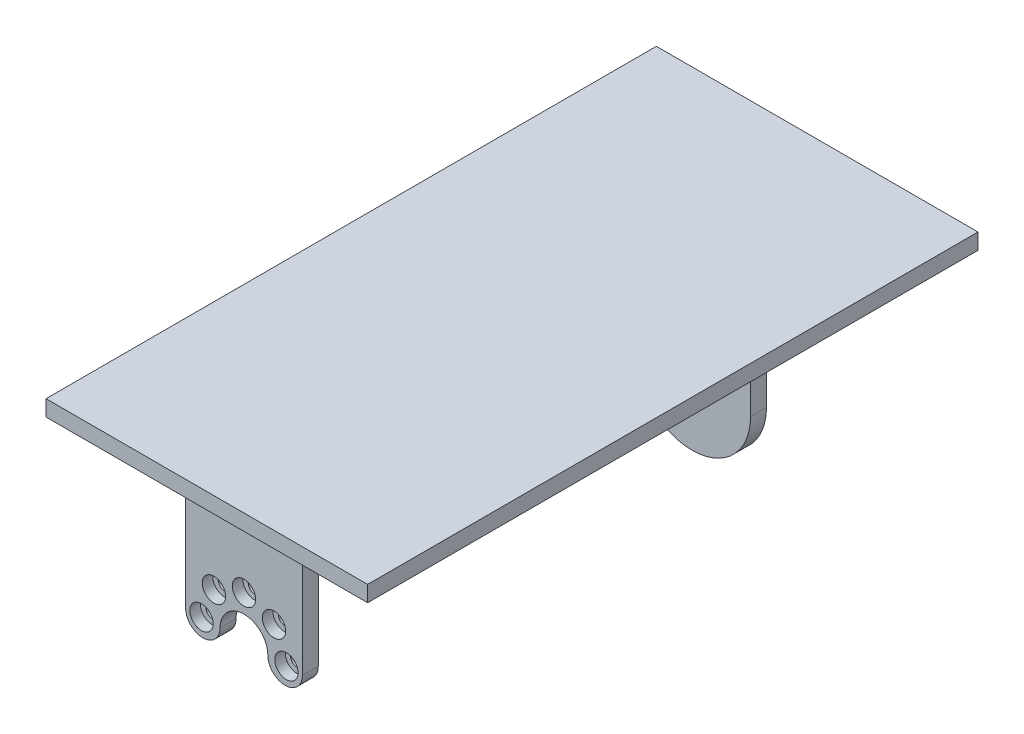
SolidWorks part; units mm, degrees
ref_plane "Plano frontal" through (0, 0, 0) normal (0, 0, 1) x (1, 0, 0)
ref_plane "Plano superior" through (0, 0, 0) normal (0, 1, 0) x (1, 0, 0)
ref_plane "Plano direito" through (0, 0, 0) normal (1, 0, 0) x (0, 0, -1)
sketch "Esboço1" plane through (0, 0, 0) normal (0, 0, 1) x (1, 0, 0)
  line L0 (11, 0) -> (11, 25)
  line L1 (11, 25) -> (-11, 25)
  line L2 (-11, 25) -> (-11, 0)
  arc A3 (11, 0) -> (4.5, 0) centre (7.75, 0) cw
  arc A8 (4.5, 0) -> (-4.5, 0) centre (0, 0) ccw
  arc A10 (-4.5, 0) -> (-11, 0) centre (-7.75, 0) cw
  dimension "D1" = 25
extrude "Ressalto-extrusão1" add sketch "Esboço1" along normal blind 3
sketch "Esboço2" plane through (0, 25, 0) normal (0, 1, 0) x (1, 0, 0)
  line L1 (-30.3, -10) -> (30.3, -10)
  line L2 (-30.3, -10) -> (-30.3, 105)
  line L3 (-30.3, 105) -> (30.3, 105)
  line L4 (30.3, -10) -> (30.3, 105)
  line L5 (11, -3) -> (-11, -3) construction
  point P7 (0, -3)
  point P8 (0, -10)
  dimension "D1" = 115
  dimension "D2" = 60.6
  dimension "D3" = 7
extrude "Ressalto-extrusão2" add sketch "Esboço2" along normal blind 3
ref_plane "Plano1" through (0, 0, -81.45) normal (0, 0, -1) x (-1, 0, 0)
sketch "Esboço3" plane through (0, 0, -81.45) normal (0, 0, -1) x (-1, 0, 0)
  line L1 (-11, 0) -> (-11, 25)
  line L2 (-11, 25) -> (11, 25)
  line L3 (11, 25) -> (11, 0)
  arc A0 (-11, 0) -> (11, 0) centre (0, 0) ccw
  dimension "D1" = 22
extrude "Ressalto-extrusão3" add sketch "Esboço3" along normal blind 3
hole_wizard "Rebaixo para SHCS M21" positions "Esboço4" profile "Esboço5" counterbore size "M2" standard "Ansi Metric"
sketch "Esboço4" plane through (0, 0, 3) normal (0, 0, 1) x (1, 0, 0)
  arc A0 (8.8, 0) -> (7.2, 0) centre (8, 0) ccw construction
  point P0 (8, 0)
sketch "Esboço5" plane through (8, 0, 3) normal (1, 0, 0) x (0, -1, 0)
  line L0 (0, 0) -> (0, 3)
  line L1 (0, 3) -> (1.2, 3)
  line L3 (1.2, 3) -> (1.2, 2)
  line L4 (1.2, 2) -> (2.2, 2)
  line L5 (2.2, 2) -> (2.2, 0)
  line L7 (2.2, 0) -> (0, 0)
  line L11 (0, -6.35) -> (0, 107.95) construction
  dimension "Thru Hole Dia." = 2.4
  dimension "Thru Hole Depth" = 3
  dimension "C'Bore Dia." = 4.4
  dimension "C'Bore Depth" = 2
pattern_circular "PadrãoCircular1" count 5 over 180 about axis through (0, 0, 0) along (0, 0, 1) of "Rebaixo para SHCS M21"
sketch "Esboço6" plane through (0, 0, 0) normal (1, 0, 0) x (0, 0, -1)
  line L0 (-10, 25) -> (-3, 25) construction
  line L3 (-3, 25) -> (-3, 18) construction
  line L4 (-3, 0) -> (-3, 25) construction
  line L5 (-3, 18) -> (-10, 25)
rib "Nervura1" sketch "Esboço6" sketch "Esboço6" thickness 15 extrusion direction parallel to sketch draft on no parameters "D1"=15
sketch "Esboço7" plane through (0, 0, 3) normal (0, 0, 1) x (1, 0, 0)
  line L0 (-7.5, 25) -> (7.5, 25) construction
  line L1 (-5, 25) -> (5, 25)
  line L2 (-5, 25) -> (-5, 18)
  line L3 (-5, 18) -> (5, 18)
  line L4 (5, 25) -> (5, 18)
  line L5 (7.5, 18) -> (-7.5, 18) construction
  point P8 (0, 18)
  point P9 (0, 18)
  dimension "D1" = 10
extrude "Corte-extrusão1" cut sketch "Esboço7" along normal up to surface (7 mm away)
sketch "Esboço8" plane through (0, 0, 0) normal (1, 0, 0) x (0, 0, -1)
  line L0 (0, 18) -> (7, 25)
  line L1 (0, 0) -> (0, 25) construction
  line L2 (-10, 25) -> (105, 25) construction
  line L5 (-10, 25) -> (-3, 18) construction
rib "Nervura7" sketch "Esboço8" sketch "Esboço8" thickness 15 extrusion direction parallel to sketch draft on no parameters "D1"=15
sketch "Esboço9" plane through (0, 0, 0) normal (0, 0, -1) x (-1, 0, 0)
  line L0 (-7.5, 18) -> (7.5, 18) construction
  line L1 (-5, 18) -> (5, 18)
  line L2 (-5, 18) -> (-5, 25)
  line L3 (-5, 25) -> (5, 25)
  line L4 (5, 18) -> (5, 25)
  line L5 (-11, 25) -> (-7.5, 25) construction
  point P8 (0, 18)
  point P9 (0, 18)
  dimension "D1" = 10
extrude "Corte-extrusão2" cut sketch "Esboço9" along normal up to surface up to face at (0, 21.5, -3.5)
pattern_linear "Padrão linear1" count 2 spacing 84.45 along (0, 0, -1) of "Nervura1", "Nervura7", "Corte-extrusão2", "Corte-extrusão1"
sketch "Esboço10" plane through (0, 0, -81.45) normal (0, 0, 1) x (1, 0, 0)
  circle A0 centre (0, 0) radius 2.75
  circle A2 centre (0, 0) radius 3.25 construction
  dimension "D1" = 0.5
extrude "Ressalto-extrusão4" add sketch "Esboço10" along normal offset from surface (0.6 mm away) 0.25 contours A0
hole_wizard "Rebaixo para parafuso com cabeça panela de M31" positions "Esboço11" profile "Esboço12" counterbore size "M3" standard "DIN" end condition up to next
sketch "Esboço11" plane through (0, 0, -84.45) normal (0, 0, -1) x (-1, 0, 0)
  circle A0 centre (0, 0) radius 3.25 construction
  point P0 (0, 0)
sketch "Esboço12" plane through (0, 0, -84.45) normal (1, 0, 0) x (0, 1, 0)
  line L0 (0, 0) -> (0, 3.6)
  line L1 (0, 3.6) -> (1.7, 3.6)
  line L3 (1.7, 3.6) -> (1.7, 1.5)
  line L4 (1.7, 1.5) -> (3.5, 1.5)
  line L5 (3.5, 1.5) -> (3.5, 0)
  line L7 (3.5, 0) -> (0, 0)
  line L11 (0, -6.35) -> (0, 107.95) construction
  dimension "Thru Hole Dia." = 3.4
  dimension "Thru Hole Depth" = 3.6
  dimension "C'Bore Dia." = 7
  dimension "C'Bore Depth" = 1.5
